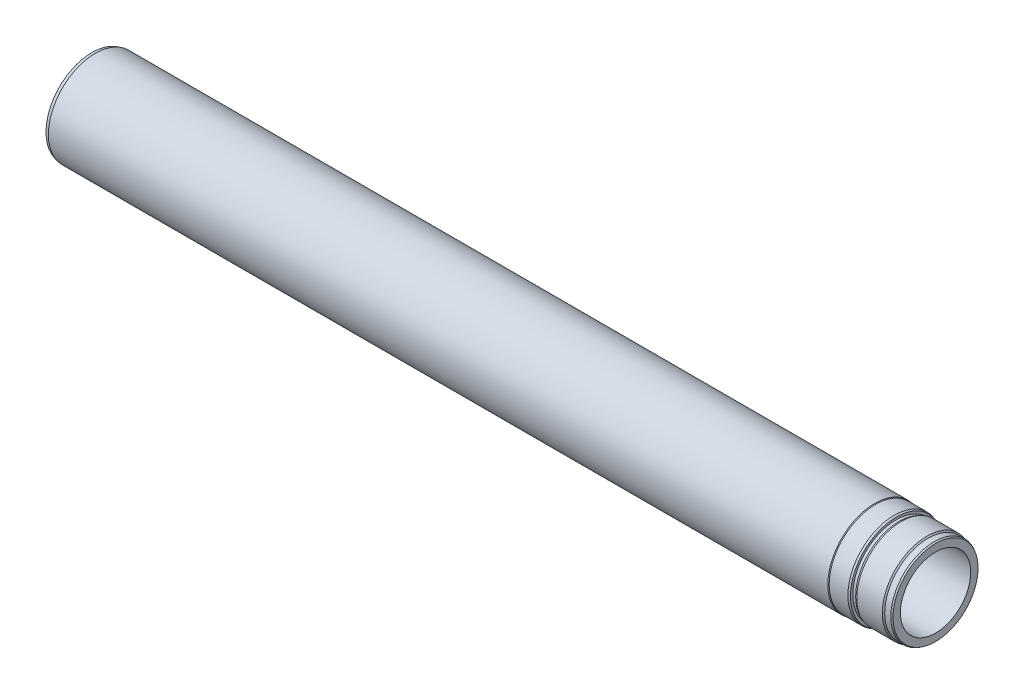
SolidWorks part; units mm, degrees
ref_plane "Front" through (0, 0, 0) normal (0, 0, 1) x (1, 0, 0)
ref_plane "Top" through (0, 0, 0) normal (0, 1, 0) x (1, 0, 0)
ref_plane "Right" through (0, 0, 0) normal (1, 0, 0) x (0, 0, -1)
sketch "Sketch1" plane through (0, 0, 0) normal (0, 0, 1) x (1, 0, 0)
  line L0 (-900, 0) -> (0, 0) construction
  line L1 (0, 37.5) -> (0, 45.384)
  line L2 (-1.5, 46.25) -> (-8, 46.25)
  line L3 (-8, 46.25) -> (-9.25, 47.5)
  line L4 (-64.866, 50) -> (-896.5, 50)
  line L5 (-896.5, 50) -> (-900, 49.0622)
  line L6 (-898.5, 40.25) -> (-878, 40.25)
  line L7 (-900, 49.0622) -> (-900, 41.75)
  line L8 (-816.961, 37.5) -> (0, 37.5)
  line L9 (-9.25, 47.5) -> (-36.5467, 47.5)
  line L10 (-42, 48.7721) -> (-42, 46.25)
  line L11 (-44, 49.5) -> (-64, 49.5)
  line L12 (-64, 49.5) -> (-64.866, 50)
  line L13 (-42, 46.25) -> (-39, 46.25)
  line L14 (-39, 46.25) -> (-36.5467, 47.5)
  line L15 (-1.5, 46.25) -> (0, 45.384)
  line L16 (-42, 48.7721) -> (-44, 49.5)
  line L17 (-900, 41.75) -> (-898.5, 40.25)
  line L19 (-878, 40.25) -> (-875.692, 38.9175)
  line L20 (-875.692, 38.9175) -> (-825, 38.9175)
  line L21 (-825, 38.9175) -> (-816.961, 37.5)
  dimension "D22" = 15
  dimension "D24" = 1.5
  dimension "D4" = 95
  dimension "D5" = 75
  dimension "D6" = 3.5
  dimension "D7" = 8
  dimension "D8" = 92.5
  dimension "D9" = 45
  dimension "D10" = 27
  dimension "D11" = 99
  dimension "D12" = 3
  dimension "D13" = 100
  dimension "D14" = 900
  dimension "D15" = 30
  dimension "D16" = 64
  dimension "D17" = 42
  dimension "D18" = 1.5
  dimension "D19" = 30
  dimension "D20" = 92.5
  dimension "D21" = 2
  dimension "D23" = 80.5
  dimension "D25" = 22
  dimension "D26" = 30
  dimension "D27" = 77.835
  dimension "D28" = 20
  dimension "D29" = 10
  dimension "D30" = 75
  dimension "D31" = 45
revolve "Base-Revolve" add sketch "Sketch1" angle 360 about L0
cosmetic thread "Cosmetic Thread1" parameters "D1"=42, "D2"=80
cosmetic thread "Cosmetic Thread2" parameters "D2"=92.835
